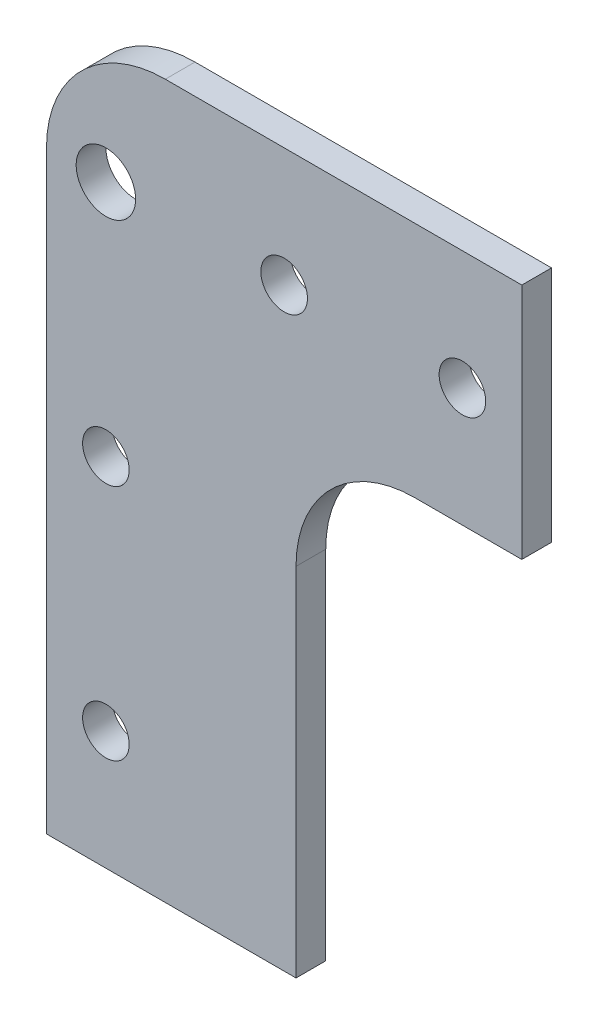
SolidWorks part; units mm, degrees
ref_plane "Front" through (0, 0, 0) normal (0, 0, 1) x (1, 0, 0)
ref_plane "Top" through (0, 0, 0) normal (0, 1, 0) x (1, 0, 0)
ref_plane "Right" through (0, 0, 0) normal (1, 0, 0) x (0, 0, -1)
sketch "Sketch1" plane through (0, 0, 0) normal (0, 0, 1) x (1, 0, 0)
  line L0 (0, 0) -> (50.8, 0)
  line L1 (50.8, 0) -> (50.8, -25.4)
  line L2 (50.8, -25.4) -> (26.67, -25.4)
  line L3 (26.67, -25.4) -> (26.67, -76.2)
  line L4 (26.67, -76.2) -> (0, -76.2)
  line L5 (0, -76.2) -> (0, 0)
  line L6 (50.8, -12.7) -> (0, -12.7) construction
  line L7 (6.35, -76.2) -> (6.35, 0) construction
  circle A0 centre (44.45, -12.7) radius 2.4892
  circle A1 centre (25.4, -12.7) radius 2.4892
  circle A2 centre (6.35, -12.7) radius 3.175
  circle A3 centre (6.35, -38.1) radius 2.4892
  circle A4 centre (6.35, -63.5) radius 2.4892
  dimension "D3" = 6.35
  dimension "D4" = 4.9784
  dimension "D1" = 25.4
  dimension "D5" = 19.05
  dimension "D6" = 19.05
  dimension "D7" = 6.35
  dimension "D8" = 25.4
  dimension "D9" = 25.4
  dimension "D10" = 12.7
  dimension "D11" = 6.35
  dimension "D2" = 26.67
extrude "Boss-Extrude1" add sketch "Sketch1" along normal blind 3.175
fillet "Fillet1" radius 12.7 2 edges at (0, 0, 1.5875) (26.67, -25.4, 1.5875)
equation "\"D5@Sketch1\"=\"D6@Sketch1\""
equation "\"D9@Sketch1\"=\"D8@Sketch1\""
